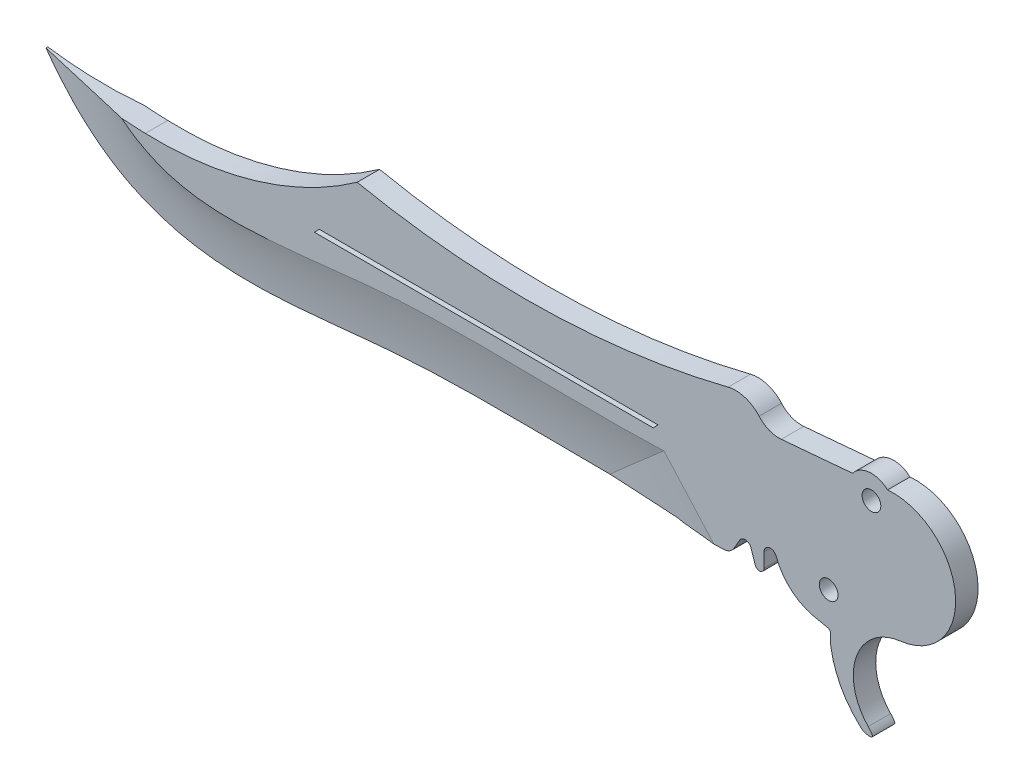
SolidWorks part; units mm, degrees
material "AISI 类型 A2 刀具钢"
ref_plane "前视基准面" through (0, 0, 0) normal (0, 0, 1) x (1, 0, 0)
ref_plane "上视基准面" through (0, 0, 0) normal (0, 1, 0) x (1, 0, 0)
ref_plane "右视基准面" through (0, 0, 0) normal (1, 0, 0) x (0, 0, -1)
sketch "Sketch1" plane through (0, 0, 0) normal (0, 0, 1) x (1, 0, 0)
  line L5 (0, 0) -> (85, -2.9683)
  line L6 (85, -2.9683) -> (-501.0754, -2.9683) construction
  line L8 (102.0768, 8.5163) -> (113.5133, 9.5169)
  line L9 (86.2404, -11.5683) -> (92.7974, -11.4182)
  line L10 (94.4835, -10.419) -> (95.3997, -8.8328)
  line L11 (97.2138, -9.0153) -> (97.8901, -11.0338)
  line L12 (99.2964, -10.8045) -> (99.2964, -8.5125)
  arc A23 (0, 0) -> (34, 10.2) centre (1.932, 55.3265) ccw
  arc A24 (34, 10.2) -> (93.5334, 11.5) centre (60.919, 141.258) ccw
  arc A25 (113.5133, 9.5169) -> (119.1244, 10.0078) centre (116.5412, 7.2209) ccw
  arc A26 (119.1244, 10.0078) -> (121.1865, -9.9757) centre (120, 0) cw
  arc A27 (121.1865, -9.9757) -> (116.0198, -24.4354) centre (122.1992, -18.4905) ccw
  arc A28 (92.7974, -11.4182) -> (94.4835, -10.419) centre (92.7516, -9.4188) ccw
  arc A29 (95.3997, -8.8328) -> (97.2138, -9.0153) centre (96.2656, -9.3329) cw
  arc A30 (97.8901, -11.0338) -> (99.2964, -10.8045) centre (98.5746, -10.8045) ccw
  arc A31 (99.2964, -8.5125) -> (101.2564, -8.1655) centre (100.3071, -8.5125) cw
  arc A32 (101.2564, -8.1655) -> (107.4602, -13.5201) centre (109.163, -5.2761) ccw
  arc A34 (109.9816, -16.0685) -> (114.735, -25.0641) centre (124.8346, -13.9737) ccw
  arc A37 (93.5334, 11.5) -> (98.5112, 9.9478) centre (94.7522, 6.6508) cw
  circle A39 centre (109.6712, -8.5891) radius 1.5
  arc A40 (102.0768, 8.5163) -> (98.5112, 9.9478) centre (101.7064, 12.7502) cw
  spline S0 degree 3 poles (85, -2.9683) (90.4327, -3.158) (90.32, -9.1865) (84.8642, -11.4683) knots 0 0 0 0 1 1 1 1
  spline S1 degree 3 poles (84.8642, -11.4683) (85.4124, -11.5511) (85.6537, -11.5817) (86.2404, -11.5683) knots 0 0 0 0 1 1 1 1
  spline S2 degree 3 poles (116.0198, -24.4354) (117.2435, -25.7073) (115.6589, -25.7249) (115.1897, -25.4782) (114.735, -25.0641) knots 0 0 0 0 0.466396 1 1 1 1
  spline S4 degree 3 poles (109.9816, -16.0685) (109.884, -15.3763) (110.1254, -13.8277) (109.6039, -13.9628) (107.4602, -13.5201) knots 0 0 0 0 0.378864 1 1 1 1
  dimension "D1" = 2
  dimension "D4" = 3.8
  dimension "D5" = 2
  dimension "D6" = 1
  dimension "D7" = 11.5
  dimension "D8" = 5
  dimension "D9" = 3
  dimension "D14" = 8.5
  dimension "D15" = 15
  dimension "D2" = 120
  dimension "D3" = 5
  dimension "D10" = 15.81
  dimension "D11" = 6.87
  dimension "D12" = 34
  dimension "D13" = 10.2
  dimension "D16" = 8.6
extrude "Extrude1" add sketch "Sketch1" along normal mid plane 3.6
sketch "Sketch2" plane through (0, 0, -1.8) normal (0, 0, -1) x (-1, 0, 0)
  circle A0 centre (-116.5412, 7.2209) radius 1.5
  circle A1 centre (-116.5412, 7.2209) radius 3.8
  dimension "D1" = 3
extrude "Extrude2" add sketch "Sketch2" against normal blind 3.6
sketch "Sketch3" plane through (0, 0, 0) normal (0, 0, 1) x (1, 0, 0)
  line L0 (0, 0) -> (85, -2.9683) construction
  line L1 (0, 0) -> (85, -2.9683)
  arc A0 (0, 0) -> (34, 10.2) centre (1.932, 55.3265) ccw construction
  arc A2 (0, 0) -> (-17.5851, 2.2507) centre (3.3532, 96.0224) cw
  spline S0 degree 3 poles (-17.5851, 2.2507) (-2.2715, -19.2457) (34.2662, -9.4251) (69.3569, -12.2738) (84.8642, -11.4683) knots 0 0 0 0 0.565859 1 1 1 1
  spline S1 degree 3 poles (-691.6416, -2892.3922) (408.4671, 2983.7235) (265.391, -3004.5448) (-619.7159, 2893.1223) knots -6.150567 -6.150567 -6.150567 -6.150567 7.381099 7.381099 7.381099 7.381099 only from (85, -2.9683) to (84.8642, -11.4683) construction
  spline S2 degree 3 poles (85, -2.9683) (90.4327, -3.158) (90.32, -9.1865) (84.8642, -11.4683) knots 0 0 0 0 1 1 1 1
sketch "Sketch4" plane through (0, 0, 1.8) normal (0, 0, 1) x (1, 0, 0)
  line L4 (27.9234, 0.6259) -> (82.3019, 0.6259)
  line L5 (27.9234, 0.6259) -> (27.1234, -0.1741)
  line L6 (82.3019, 0.6259) -> (81.5019, -0.1741)
  line L7 (27.1234, -0.1741) -> (81.5019, -0.1741)
  line L9 (1.98, 0) -> (-1.98, 0) construction
  dimension "D2" = 0.8
  dimension "D3" = 135
extrude "Extrude4" cut sketch "Sketch4" against normal through all both and the other way through all
extrude "Extrude5" add sketch "Sketch3" along normal mid plane 3.6
ref_plane "Plane6" through (0, 0, 0) normal (-0.127, -0.9919, 0) x (-0.9919, 0.127, 0)
sketch "Sketch14" plane through (0, 0, 0) normal (-0.127, -0.9919, 0) x (-0.9919, 0.127, 0)
  line L0 (19.7285, 1.8) -> (19.7285, 0.025)
  line L1 (19.7285, -0.025) -> (19.7285, -1.8)
  line L2 (17.7285, 0) -> (-1.7102, 0) construction
  line L6 (-85.6334, -1.8) -> (17.7285, -1.8) construction
  line L7 (17.7285, 1.8) -> (-85.6334, 1.8) construction
  line L9 (4.2592, -1.8) -> (19.7285, -1.8)
  line L10 (19.7285, 1.8) -> (4.2592, 1.8)
  arc A0 (19.7285, 0.025) -> (4.2592, 1.8) centre (26.8107, 130.0427) cw
  arc A1 (19.7285, -0.025) -> (4.2592, -1.8) centre (26.8107, -130.0427) ccw
  point P13 (4.2592, 0)
  dimension "D1" = 0.05
  dimension "D2" = 2
sketch "Sketch15" plane through (0, 0, 0) normal (0, 0, 1) x (1, 0, 0)
  spline S2 degree 3 poles (173.9126, 2996.8896) (-88.0468, 382.248) (-59.4043, 48.6053) (-7.265, -1.8606) (-5.6638, -3.113) (-2.3997, -5.1884) (-0.7356, -6.0123) (2.6968, -7.3273) (4.466, -7.8179) (8.1341, -8.5285) (10.0327, -8.7477) (13.9548, -8.9701) (15.9779, -8.9732) (20.1292, -8.8274) (22.2571, -8.6786) (26.5963, -8.3033) (28.8075, -8.077) (33.2952, -7.6284) (35.5716, -7.4062) (39.0251, -7.1418) (40.1766, -7.0664) (42.4688, -6.9386) (43.6114, -6.886) (49.3071, -6.6711) (53.8089, -6.6517) (62.7254, -6.6967) (67.1404, -6.761) (203.65, -6.7897) (308.3368, 50.6597) (808.293, 2894.724) knots -1.937428 -1.937428 -1.937428 -1.937428 0.0625 0.0625 0.125 0.125 0.1875 0.1875 0.25 0.25 0.3125 0.3125 0.375 0.375 0.4375 0.4375 0.5 0.5 0.5625 0.5625 0.59375 0.59375 0.625 0.625 0.75 0.75 0.875 0.875 4.641472 4.641472 4.641472 4.641472 only from (-13.5128, 5.1517) to (84.6048, -6.475)
  spline S3 degree 3 poles (-13.5128, 5.1517) (-11.9837, 3.0054) (-10.4251, 1.198) (-7.265, -1.8606) (-5.6638, -3.113) (-2.3997, -5.1884) (-0.7356, -6.0123) (2.6968, -7.3273) (4.466, -7.8179) (8.1341, -8.5285) (10.0327, -8.7477) (13.9548, -8.9701) (15.9779, -8.9732) (20.1292, -8.8274) (22.2571, -8.6786) (26.5963, -8.3033) (28.8075, -8.077) (33.2952, -7.6284) (35.5716, -7.4062) (39.0251, -7.1418) (40.1766, -7.0664) (42.4688, -6.9386) (43.6114, -6.886) (49.3071, -6.6711) (53.8089, -6.6517) (62.7254, -6.6967) (67.1404, -6.761) (73.8751, -6.7624) (76.2163, -6.7447) (78.5511, -6.6935) knots 0 0 0 0 0.0625 0.0625 0.125 0.125 0.1875 0.1875 0.25 0.25 0.3125 0.3125 0.375 0.375 0.4375 0.4375 0.5 0.5 0.5625 0.5625 0.59375 0.59375 0.625 0.625 0.75 0.75 0.875 0.875 0.941987 0.941987 0.941987 0.941987
  dimension "D1" = 5
sweep "Cut-Sweep7" cut profiles "Sketch14" path "Sketch15"
sketch "Sketch19" plane through (38.205, -42.7501, 0) normal (-0.6664, 0.7456, 0) x (0.7456, 0.6664, 0)
  line L0 (46.5066, -1.8) -> (60.3953, -1.8) construction
  line L1 (46.5066, -0.1207) -> (46.5066, -1.8) construction
  line L2 (46.5066, 1.8) -> (46.5066, 0.1207) construction
  line L3 (60.3953, 1.8) -> (46.5066, 1.8) construction
  line L4 (46.5066, -1.8) -> (60.3953, -1.8)
  line L5 (46.5066, -0.1207) -> (46.5066, -1.8)
  line L6 (46.5066, 1.8) -> (46.5066, 0.1207)
  line L7 (60.3953, 1.8) -> (46.5066, 1.8)
  arc A0 (60.3953, -1.8) -> (46.5066, -0.1207) centre (37.8438, -130.0427) ccw construction
  arc A1 (46.5066, 0.1207) -> (60.3953, 1.8) centre (37.8438, 130.0427) ccw construction
  arc A2 (60.3953, -1.8) -> (46.5066, -0.1207) centre (37.8438, -130.0427) ccw
  arc A3 (46.5066, 0.1207) -> (60.3953, 1.8) centre (37.8438, 130.0427) ccw
extrude "Extrude6" cut sketch "Sketch19" against normal blind 15.6
